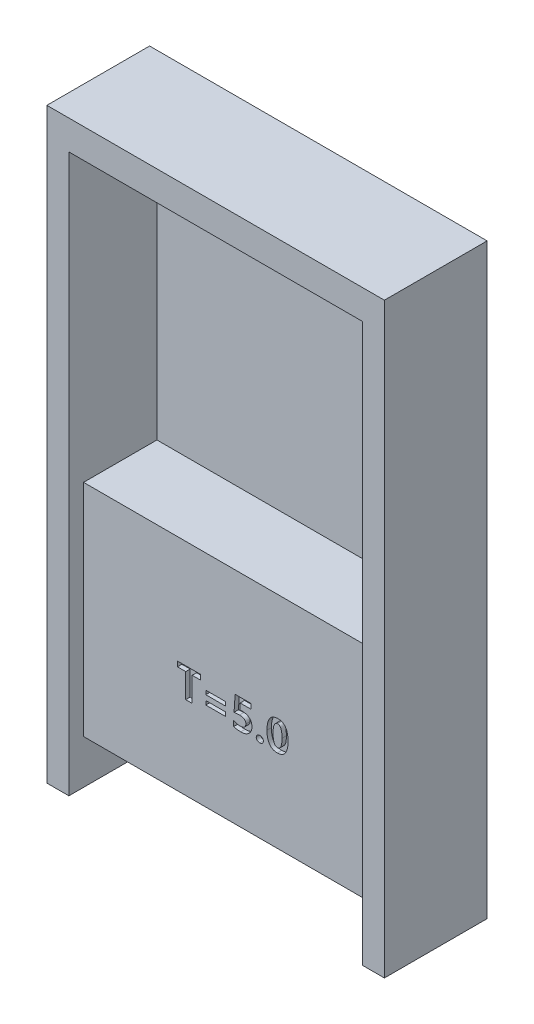
SolidWorks part; units mm, degrees
ref_plane "前视基准面" through (0, 0, 0) normal (0, 0, 1) x (1, 0, 0)
ref_plane "上视基准面" through (0, 0, 0) normal (0, 1, 0) x (1, 0, 0)
ref_plane "右视基准面" through (0, 0, 0) normal (1, 0, 0) x (0, 0, -1)
sketch "草图1" plane through (0, 0, 0) normal (0, 0, 1) x (1, 0, 0)
  line L0 (-1020, 0) -> (-11.5, 0) construction
  line L1 (0, 0) -> (0, 25.9672) construction
  line L2 (-10, 0) -> (-10, -18)
  line L4 (-10, 0) -> (-10, 20)
  line L5 (-10, 20) -> (10, 20)
  line L6 (10, 0) -> (10, 20)
  line L8 (10, -18) -> (10, 0)
  line L10 (-11.5, 22) -> (11.5, 22)
  line L11 (-11.5, 22) -> (-11.5, -18)
  line L12 (-11.5, -18) -> (-10, -18)
  line L13 (11.5, 22) -> (11.5, -18)
  line L15 (10, -18) -> (11.5, -18)
  line L16 (11.5, 0) -> (1020.3279, 0) construction
  point P2 (0, 20)
  point P16 (0, 22)
  point P21 (0, 0)
  point P22 (0, 0)
  point P23 (0, 0)
  point P24 (0, 0)
  dimension "D1" = 20
  dimension "D2" = 20
  dimension "D4" = 23
  dimension "D5" = 40
  dimension "D6" = 22
extrude "凸台-拉伸1" add sketch "草图1" along normal blind 7
sketch "草图2" plane through (0, 0, 0) normal (0, 0, 1) x (1, 0, 0)
  line L0 (0, 0) -> (32.0423, 0) construction
  line L1 (10, 20) -> (10, -18) construction
  line L2 (0, 0) -> (0, 18.5674) construction
  line L3 (-10, 20) -> (10, 20)
  line L4 (-10, 20) -> (-10, -15)
  line L5 (-10, -15) -> (10, -15)
  line L6 (10, 20) -> (10, -15)
  dimension "D1" = 35
extrude "凸台-拉伸2" add sketch "草图2" along normal blind 6
sketch "草图3" plane through (0, 0, 6) normal (0, 0, 1) x (1, 0, 0)
  line L0 (-10, 0) -> (10, 0)
  line L1 (-10, 20) -> (-10, -15) construction
  line L2 (10, -15) -> (10, 20) construction
  line L3 (-10, 0) -> (-10, 20)
  line L4 (-10, 20) -> (10, 20)
  line L5 (10, 20) -> (10, 0)
extrude "切除-拉伸1" cut sketch "草图3" against normal blind 5
sketch "草图4" plane through (0, 0, 0) normal (0, 0, -1) x (-1, 0, 0)
  line L0 (0, 0) -> (0, 18.3654) construction
  line L1 (-7, -2) -> (7, -2)
  line L2 (-7, -2) -> (-7, -12)
  line L3 (-7, -12) -> (7, -12)
  line L4 (7, -2) -> (7, -12)
  line L5 (10, -15) -> (-10, -15) construction
  line L6 (10, 0) -> (-10, 0) construction
  point P5 (0, -2)
  dimension "D1" = 2
  dimension "D2" = 14
  dimension "D3" = 3
extrude "切除-拉伸2" cut sketch "草图4" against normal blind 5
sketch "草图5" plane through (0, 0, 6) normal (0, 0, 1) x (1, 0, 0)
  text T0 "T=5.0" font "微软雅黑" height 2
extrude "切除-拉伸3" cut sketch "草图5" against normal blind 0.3
